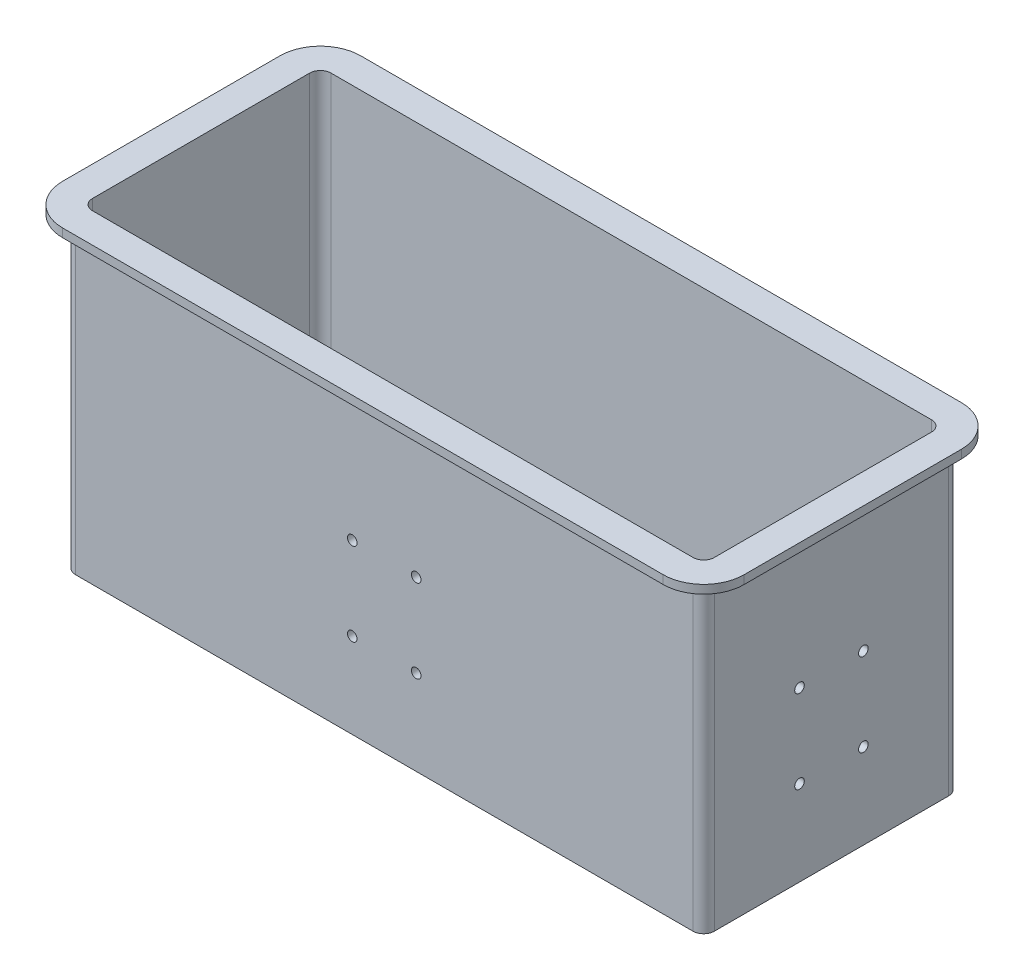
SolidWorks part; units mm, degrees
ref_plane "Front Plane" through (0, 0, 0) normal (0, 0, 1) x (1, 0, 0)
ref_plane "Top Plane" through (0, 0, 0) normal (0, 1, 0) x (1, 0, 0)
ref_plane "Right Plane" through (0, 0, 0) normal (1, 0, 0) x (0, 0, -1)
sketch "Sketch1" plane through (0, 0, 0) normal (0, 1, 0) x (1, 0, 0)
  line L0 (150, -60) -> (-150, 60) construction
  line L1 (-150, 60) -> (150, 60)
  line L2 (-150, 60) -> (-150, -60)
  line L3 (-150, -60) -> (150, -60)
  line L4 (150, 60) -> (150, -60)
  line L5 (-150, -60) -> (150, 60) construction
  point P7 (0, 0)
  dimension "D1" = 300
  dimension "D2" = 120
extrude "Boss-Extrude1" add sketch "Sketch1" along normal blind 4
sketch "Sketch2" plane through (0, 4, 0) normal (0, 1, 0) x (1, 0, 0)
  line L0 (-146, 56) -> (-150, 56) construction
  line L1 (-150, -60) -> (150, -60)
  line L2 (-150, -60) -> (-150, 60)
  line L3 (-150, 60) -> (150, 60)
  line L4 (150, -60) -> (150, 60)
  line L5 (-146, -56) -> (146, -56)
  line L6 (-146, -56) -> (-146, 56)
  line L7 (-146, 56) -> (146, 56)
  line L8 (146, -56) -> (146, 56)
  line L9 (-146, 56) -> (-146, 60) construction
  line L10 (146, -56) -> (146, -60) construction
  line L11 (146, -60) -> (146, -56) construction
  line L12 (146, -56) -> (150, -56) construction
  dimension "D1" = 4
extrude "Boss-Extrude2" add sketch "Sketch2" along normal blind 140
fillet "Fillet1" radius 5 8 edges at (-150, 72, 60) (150, 72, 60) (150, 72, -60) (-150, 72, -60) (146, 74, 56) (-146, 74, 56) (-146, 74, -56) (146, 74, -56)
sketch "Sketch3" plane through (0, 144, 0) normal (0, 1, 0) x (1, 0, 0)
  line L0 (-141, 56) -> (141, 56)
  line L1 (146, 51) -> (146, -51)
  line L2 (141, -56) -> (-141, -56)
  line L3 (-146, -51) -> (-146, 51)
  line L4 (146, -51) -> (146, 51) construction
  line L5 (-141, -56) -> (141, -56) construction
  line L6 (-146, 51) -> (-146, -51) construction
  line L7 (-141, 70) -> (141, 70)
  line L8 (160, 51) -> (160, -51)
  line L9 (141, -70) -> (-141, -70)
  line L10 (-160, -51) -> (-160, 51)
  arc A0 (-141, 56) -> (-146, 51) centre (-141, 51) ccw
  arc A1 (-141, -56) -> (-146, -51) centre (-141, -51) cw
  arc A2 (146, -51) -> (141, -56) centre (141, -51) cw
  arc A3 (141, 56) -> (146, 51) centre (141, 51) cw
  arc A4 (141, 70) -> (160, 51) centre (141, 51) cw
  arc A5 (160, -51) -> (141, -70) centre (141, -51) cw
  arc A6 (-141, -70) -> (-160, -51) centre (-141, -51) cw
  arc A7 (-141, 70) -> (-160, 51) centre (-141, 51) ccw
  dimension "D1" = 5
  dimension "D2" = 14
extrude "Boss-Extrude3" add sketch "Sketch3" along normal blind 4
fillet "Fillet2" radius 2 8 edges at (0, 144, -60) (148.5355, 144, -58.5355) (150, 144, 0) (148.5355, 144, 58.5355) (0, 144, 60) (-148.5355, 144, 58.5355) (-150, 144, 0) (-148.5355, 144, -58.5355)
sketch "Sketch4" plane through (150, 0, 0) normal (1, 0, 0) x (0, 0, -1)
  line L0 (-15, 40) -> (-60, 40) construction
  line L1 (-60, 0) -> (-60, 142) construction
  line L2 (15, 40) -> (60, 40) construction
  line L3 (60, 142) -> (60, 0) construction
  line L4 (-15, 40) -> (0, 0) construction
  line L5 (0, 0) -> (15, 40) construction
  circle A0 centre (-15, 79) radius 2.25
  circle A1 centre (15, 79) radius 2.25
  circle A2 centre (15, 40) radius 2.25
  circle A3 centre (-15, 40) radius 2.25
  dimension "D1" = 4.5
  dimension "D2" = 39
  dimension "D3" = 30
  dimension "D4" = 40
extrude "Cut-Extrude1" cut sketch "Sketch4" against normal up to next
sketch "Sketch5" plane through (0, 0, 60) normal (0, 0, 1) x (1, 0, 0)
  line L0 (-15, 40) -> (0, 0) construction
  line L1 (0, 0) -> (15, 40) construction
  line L2 (-145, 0) -> (145, 0) construction
  circle A0 centre (15, 79) radius 2.25
  circle A1 centre (-15, 79) radius 2.25
  circle A2 centre (-15, 40) radius 2.25
  circle A3 centre (15, 40) radius 2.25
  dimension "D1" = 4.5
  dimension "D2" = 40
  dimension "D3" = 30
  dimension "D4" = 39
extrude "Cut-Extrude2" cut sketch "Sketch5" against normal up to next
